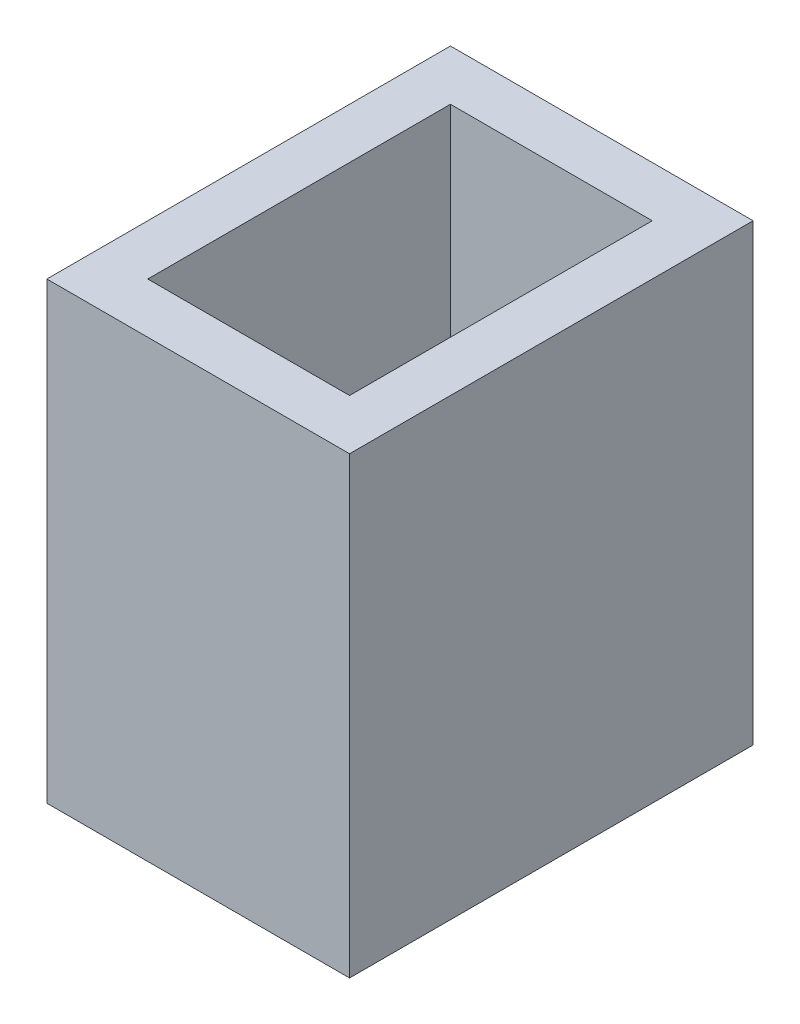
SolidWorks part; units mm, degrees
ref_plane "Front Plane" through (0, 0, 0) normal (0, 0, 1) x (1, 0, 0)
ref_plane "Top Plane" through (0, 0, 0) normal (0, 1, 0) x (1, 0, 0)
ref_plane "Right Plane" through (0, 0, 0) normal (1, 0, 0) x (0, 0, -1)
sketch "Sketch1" plane through (0, 0, 0) normal (0, 1, 0) x (1, 0, 0)
  line L1 (0, 0) -> (12, 0)
  line L2 (0, 0) -> (0, 16)
  line L3 (0, 16) -> (12, 16)
  line L4 (12, 0) -> (12, 16)
  dimension "D1" = 12
  dimension "D2" = 16
extrude "Boss-Extrude1" add sketch "Sketch1" along normal blind 18
shell "Shell1" thickness 2
sketch "Sketch2" plane through (0, 0, 0) normal (0, -1, 0) x (1, 0, 0)
  circle A0 centre (4.7701, -4.1638) radius 0.75
  circle A1 centre (4.7701, -6.7038) radius 0.75
  circle A2 centre (4.7701, -11.7838) radius 0.75
  point P0 (4.7701, -4.1638)
  point P1 (4.7701, -6.7038)
  point P2 (4.7701, -11.7838)
  dimension "D1" = 1.5
  dimension "D2" = 1.5
  dimension "D3" = 1.5
extrude "Cut-Extrude1" cut sketch "Sketch2" against normal blind 10
